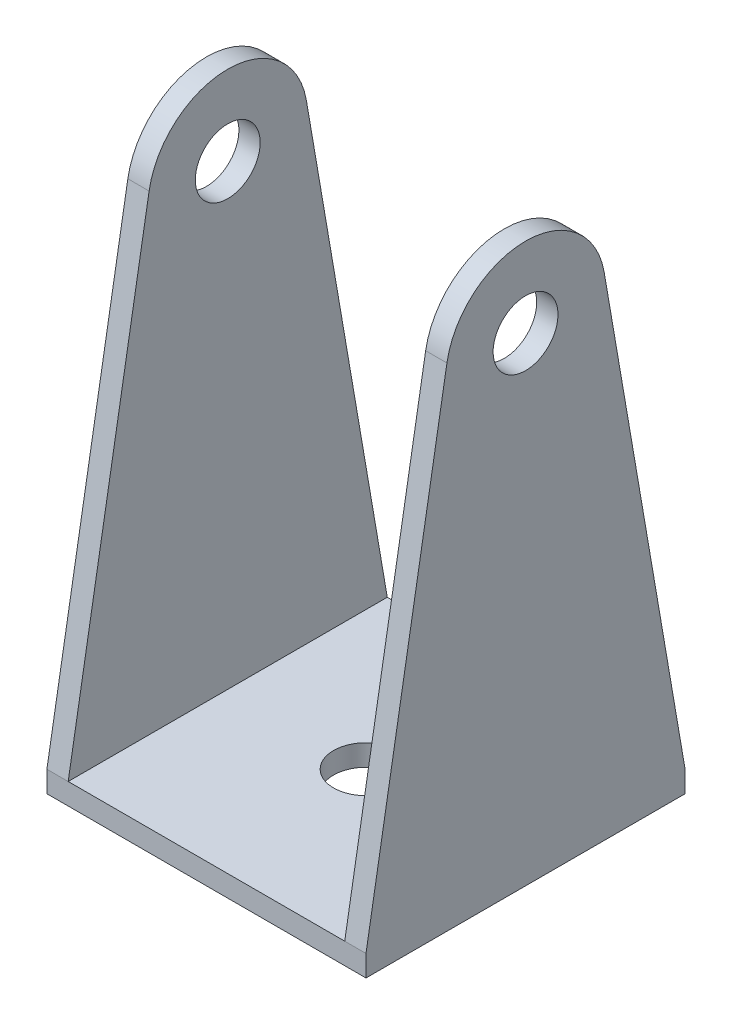
SolidWorks part; units mm, degrees
material "6061 合金"
ref_plane "前视基准面" through (0, 0, 0) normal (0, 0, 1) x (1, 0, 0)
ref_plane "上视基准面" through (0, 0, 0) normal (0, 1, 0) x (1, 0, 0)
ref_plane "右视基准面" through (0, 0, 0) normal (1, 0, 0) x (0, 0, -1)
sketch "草图1" plane through (0, 0, 0) normal (0, 0, 1) x (1, 0, 0)
  line L0 (-25.3132, 0) -> (25.4167, 0) construction
  line L1 (0, 42.3624) -> (0, -24.8288) construction
  line L2 (-13, -20.7978) -> (-13, -73.7978)
  line L3 (-15, -20.7978) -> (-13, -20.7978)
  line L4 (-15, -20.7978) -> (-15, -75.7978)
  line L5 (-15, -75.7978) -> (15, -75.7978)
  line L6 (15, -20.7978) -> (15, -75.7978)
  line L7 (-13, -73.7978) -> (13, -73.7978)
  line L8 (13, -73.7978) -> (13, -20.7978)
  line L9 (13, -20.7978) -> (15, -20.7978)
  dimension "D1" = 2
  dimension "D2" = 2
  dimension "D3" = 55
  dimension "D4" = 30
extrude "凸台-拉伸1" add sketch "草图1" along normal blind 30
sketch "草图2" plane through (0, -75.7978, 0) normal (0, -1, 0) x (1, 0, 0)
  line L0 (-22.7426, 15) -> (24.974, 15) construction
  line L1 (-15, 30) -> (-15, 0) construction
  line L2 (0, 31.698) -> (0, -9.3817) construction
  line L3 (15, 30) -> (15, 0) construction
  line L4 (-15, 30) -> (15, 30) construction
  line L5 (-15, 0) -> (15, 0) construction
  circle A0 centre (0, 15) radius 3.05
  dimension "D1" = 6.1
extrude "切除-拉伸1" cut sketch "草图2" against normal blind 30
sketch "草图3" plane through (15, 0, 0) normal (1, 0, 0) x (0, 0, -1)
  line L0 (-15, -82.7785) -> (-15, 50.0378) construction
  line L1 (-30, -75.7978) -> (-30, -20.7978) construction
  line L2 (0, -75.7978) -> (0, -20.7978) construction
  line L3 (-30, -75.7978) -> (0, -75.7978) construction
  circle A0 centre (-15, -30.7978) radius 3.05
  dimension "D1" = 6.1
  dimension "D2" = 45
extrude "切除-拉伸2" cut sketch "草图3" against normal blind 30 contours A0
sketch "草图4" plane through (-15, 0, 0) normal (-1, 0, 0) x (0, 0, 1)
  line L0 (0, -73.7978) -> (7.6084, -29.5275)
  line L1 (30, -73.7978) -> (22.3916, -29.5275)
  line L2 (30, -20.7978) -> (30, -75.7978) construction
  line L3 (0, -20.7978) -> (30, -20.7978)
  line L4 (0, -20.7978) -> (0, -73.7978)
  line L6 (30, -20.7978) -> (30, -73.7978)
  line L7 (30, -75.7978) -> (0, -75.7978) construction
  line L8 (0, -20.7978) -> (0, -75.7978) construction
  arc A0 (22.3916, -29.5275) -> (7.6084, -29.5275) centre (15, -30.7978) ccw
  dimension "D1" = 15
  dimension "D2" = 2
  dimension "D3" = 2
extrude "切除-拉伸3" cut sketch "草图4" against normal blind 54 contours L1 A0 L0 L4 L3 L6
